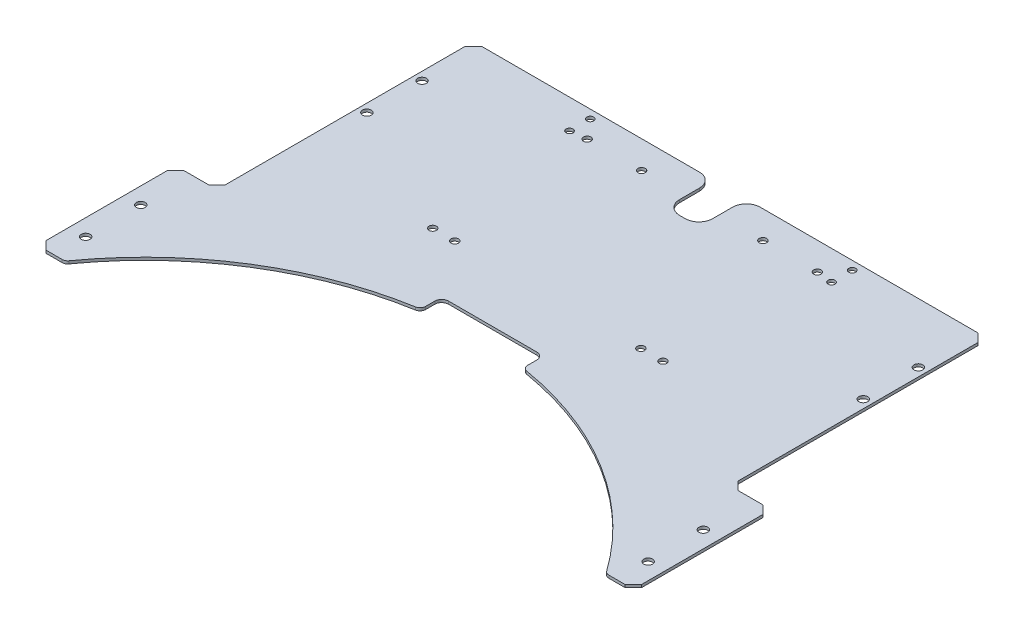
SolidWorks part; units mm, degrees
material "Hexcel AS4C (3000 丝)"
ref_plane "前视基准面" through (0, 0, 0) normal (0, 0, 1) x (1, 0, 0)
ref_plane "上视基准面" through (0, 0, 0) normal (0, 1, 0) x (1, 0, 0)
ref_plane "右视基准面" through (0, 0, 0) normal (1, 0, 0) x (0, 0, -1)
sketch "草图1" plane through (0, 0, 0) normal (0, 1, 0) x (1, 0, 0)
  line L1 (-93, 55) -> (93, 55)
  line L2 (-93, 55) -> (-93, -55)
  line L3 (-93, -55) -> (93, -55)
  line L4 (93, 55) -> (93, -55)
  line L5 (0, -55) -> (0, 55) construction
  line L6 (-93, 0) -> (93, 0) construction
  point P0 (0, 0)
  dimension "D1" = 186
  dimension "D2" = 110
extrude "凸台-拉伸1" add sketch "草图1" along normal blind 1
sketch "草图2" plane through (0, 1, 0) normal (0, 1, 0) x (1, 0, 0)
  line L0 (0, -55) -> (0, -50055) construction
  line L1 (-93, -55) -> (93, -55) construction
  line L2 (90, 55) -> (90, -49945) construction
  line L4 (93, -55) -> (93, 55) construction
  circle A0 centre (90, 15.38) radius 1.6
  circle A1 centre (90, 35.38) radius 1.6
  circle A2 centre (-90, 35.38) radius 1.6
  circle A3 centre (-90, 15.38) radius 1.6
  point P4 (0, -55)
  dimension "D2" = 20
  dimension "3.2" = 3.2
  dimension "D1" = 3
  dimension "D3" = 70.38
extrude "切除-拉伸1" cut sketch "草图2" against normal through all
sketch "草图3" plane through (0, 1, 0) normal (0, 1, 0) x (1, 0, 0)
  line L0 (0, 55) -> (0, -49945) construction
  line L1 (93, 55) -> (-93, 55) construction
  circle A0 centre (0, -155.12) radius 120 construction
  point P4 (0, 55)
  dimension "D1" = 240
  dimension "D2" = 210.12
sketch "草图5" plane through (0, 1, 0) normal (0, 1, 0) x (1, 0, 0)
  line L0 (0, 55) -> (0, -49945) construction
  line L1 (93, 55) -> (-93, 55) construction
  line L2 (-108, -86) -> (108, -86)
  line L3 (-93, -36) -> (-108, -36)
  line L4 (-93, 55) -> (-93, -55) construction
  line L5 (-108, -36) -> (-108, -86)
  line L6 (-93, -36) -> (-93, -55)
  line L7 (-93, -55) -> (93, -55)
  line L8 (-93, -55) -> (93, -55) construction
  line L9 (93, -36) -> (93, -55)
  line L10 (108, -36) -> (108, -86)
  line L11 (93, -36) -> (108, -36)
  point P4 (0, 55)
  point P17 (0, -55)
  point P20 (0, -86)
  dimension "D1" = 15
  dimension "D2" = 50
  dimension "D3" = 19
extrude "凸台-拉伸2" add sketch "草图5" against normal up to surface (1 mm away) up to face at (-90, 0, -16.98)
sketch "草图6" plane through (0, 1, 0) normal (0, 1, 0) x (1, 0, 0)
  circle A0 centre (0, -155.12) radius 120 construction
  circle A1 centre (0, -155.12) radius 120
extrude "切除-拉伸2" cut sketch "草图6" against normal through all
sketch "草图8" plane through (0, 1, 0) normal (0, 1, 0) x (1, 0, 0)
  line L0 (93, 55) -> (-93, 55)
  line L1 (93, 55) -> (93, 57)
  line L2 (-93, 55) -> (-93, 57)
  line L3 (93, 57) -> (-93, 57)
  dimension "D1" = 2
extrude "凸台-拉伸3" add sketch "草图8" against normal up to surface (1 mm away) up to face at (-90, 0, -16.98)
sketch "草图7" plane through (0, 1, 0) normal (0, 1, 0) x (1, 0, 0)
  line L0 (108, -36) -> (93, -36) construction
  line L1 (0, 57) -> (0, 50057) construction
  line L2 (93, 57) -> (-93, 57) construction
  line L3 (108, -86) -> (108, -36) construction
  circle A0 centre (47.5, 46.38) radius 1.25 construction
  circle A1 centre (47.5, 53.88) radius 1.25 construction
  circle A4 centre (47.5, 46.38) radius 1.25
  circle A5 centre (47.5, 53.88) radius 1.25
  circle A6 centre (102, -74.62) radius 1.6
  circle A7 centre (102, -54.62) radius 1.6
  circle A8 centre (-102, -54.62) radius 1.6
  circle A9 centre (-102, -74.62) radius 1.6
  circle A10 centre (-47.5, 53.88) radius 1.25
  circle A11 centre (-47.5, 46.38) radius 1.25
  point P19 (0, 57)
  dimension "D1" = 3.2
  dimension "D2" = 18.62
  dimension "D3" = 20
  dimension "D4" = 6
extrude "切除-拉伸3" cut sketch "草图7" against normal through all
chamfer "倒角1" distance 3 angle 45 8 edges at (-93, 0.5, -57) (-93, 0.5, 36) (-108, 0.5, 36) (-108, 0.5, 86) (108, 0.5, 86) (108, 0.5, 36) (93, 0.5, 36) (93, 0.5, -57)
fillet "圆角1" radius 2 2 edges at (98.094, 0.5, 86) (-98.094, 0.5, 86)
sketch "草图9" plane through (0, 1, 0) normal (0, 1, 0) x (1, 0, 0)
  line L0 (16, -31.5) -> (-16, -31.5) construction
  line L2 (16, -29) -> (-16, -29)
  line L3 (90, 57) -> (-90, 57) construction
  line L4 (0, 200055) -> (0, -249945) construction
  line L5 (18.5, -31.5) -> (18.5, -36.5546)
  line L6 (0, 0) -> (0, -76.6319) construction
  line L7 (-18.5, -31.5) -> (-18.5, -36.5546)
  circle A0 centre (0, -155.12) radius 120 construction
  arc A1 (18.5, -36.5546) -> (-18.5, -36.5546) centre (0, -155.12) ccw
  circle A5 centre (14, -31.87) radius 0.5 construction
  circle A6 centre (10, -31.87) radius 0.5 construction
  circle A7 centre (6, -31.87) radius 0.5 construction
  circle A8 centre (-8, -31.87) radius 0.5 construction
  circle A9 centre (-12, -31.87) radius 0.5 construction
  arc A10 (18.5, -31.5) -> (16, -29) centre (16, -31.5) ccw
  arc A11 (-16, -29) -> (-18.5, -31.5) centre (-16, -31.5) ccw
  dimension "D1" = 2.5
  dimension "D2" = 32
  dimension "D3" = 88.5
  dimension "D4" = 16
extrude "切除-拉伸4" cut sketch "草图9" against normal through all
sketch "草图10" plane through (0, 1, 0) normal (0, 1, 0) x (1, 0, 0)
  line L0 (-33.75, -9) -> (33.75, -9) construction
  line L1 (-22, 47) -> (22, 47) construction
  line L3 (0, 0) -> (0, 122.5252) construction
  line L4 (90, 57) -> (-90, 57) construction
  circle A0 centre (-33.75, -9) radius 1.35
  circle A1 centre (-22, 47) radius 1.35
  circle A2 centre (22, 47) radius 1.35
  circle A3 centre (33.75, -9) radius 1.35
  circle A4 centre (41.75, -9) radius 1.35
  circle A5 centre (-41.75, -9) radius 1.35
  circle A6 centre (41.75, 47) radius 1.35
  circle A7 centre (-41.75, 47) radius 1.35
  dimension "D3" = 2.7
  dimension "D4" = 8
  dimension "D1" = 67.5
  dimension "D2" = 44
  dimension "D5" = 56
  dimension "D6" = 10
extrude "切除-拉伸5" cut sketch "草图10" against normal through all
sketch "草图11" plane through (0, 1, 0) normal (0, 1, 0) x (1, 0, 0)
  line L4 (0, 0) -> (0, 98.9823) construction
  line L5 (6, 39.8) -> (6, 57)
  line L6 (90, 57) -> (-90, 57) construction
  line L7 (-6, 39.8) -> (-6, 57)
  line L8 (6, 57) -> (-6, 57)
  line L9 (-6, 39.8) -> (6, 39.8)
  dimension "D1" = 12
  dimension "D2" = 17.2
extrude "切除-拉伸6" cut sketch "草图11" against normal through all
fillet "圆角2" radius 5 4 edges at (-6, 0.5, -39.8) (6, 0.5, -39.8) (6, 0.5, -57) (-6, 0.5, -57)
fillet "圆角3" radius 2 2 edges at (-18.5, 0.5, 36.5546) (18.5, 0.5, 36.5546)
